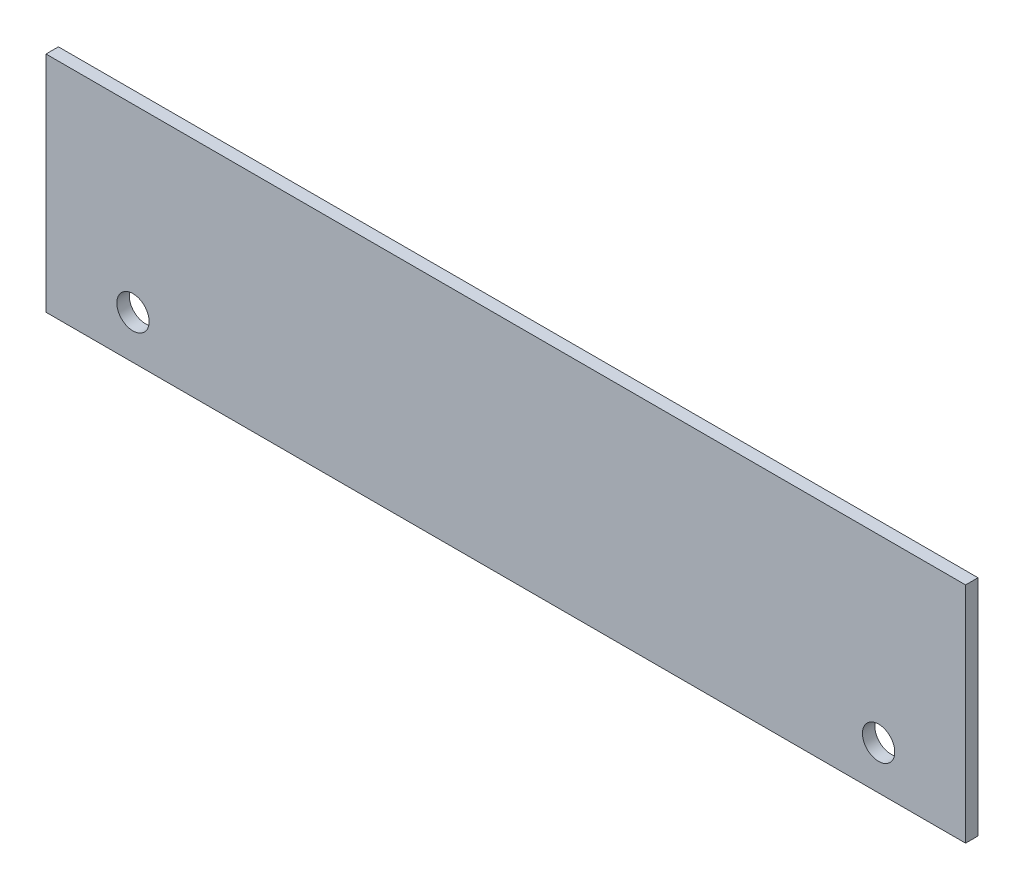
SolidWorks part; units mm, degrees
ref_plane "Front Plane" through (0, 0, 0) normal (0, 0, 1) x (1, 0, 0)
ref_plane "Top Plane" through (0, 0, 0) normal (0, 1, 0) x (1, 0, 0)
ref_plane "Right Plane" through (0, 0, 0) normal (1, 0, 0) x (0, 0, -1)
sketch "Sketch1" plane through (0, 0, 0) normal (0, 0, 1) x (1, 0, 0)
  line L1 (-185, 45) -> (185, 45)
  line L2 (-185, 45) -> (-185, -45)
  line L3 (-185, -45) -> (185, -45)
  line L4 (185, 45) -> (185, -45)
  line L5 (-185, 45) -> (185, -45) construction
  line L6 (-185, -45) -> (185, 45) construction
  point P0 (0, 0)
  dimension "D1" = 370
  dimension "D2" = 90
extrude "Boss-Extrude1" add sketch "Sketch1" along normal blind 5
sketch "Sketch2" plane through (0, 0, 5) normal (0, 0, 1) x (1, 0, 0)
  line L0 (185, -45) -> (185, -27.5)
  line L1 (185, -45) -> (185, 45) construction
  line L5 (185, -45) -> (165, -45)
  line L6 (-185, -45) -> (185, -45) construction
  circle A0 centre (150, -27.5) radius 6.5
  circle A4 centre (-150, -27.5) radius 6.5
  dimension "D3" = 13
  dimension "D4" = 35
  dimension "D1" = 17.5
  dimension "D2" = 20
extrude "Cut-Extrude1" cut sketch "Sketch2" against normal blind 10 contours A4 | A0
